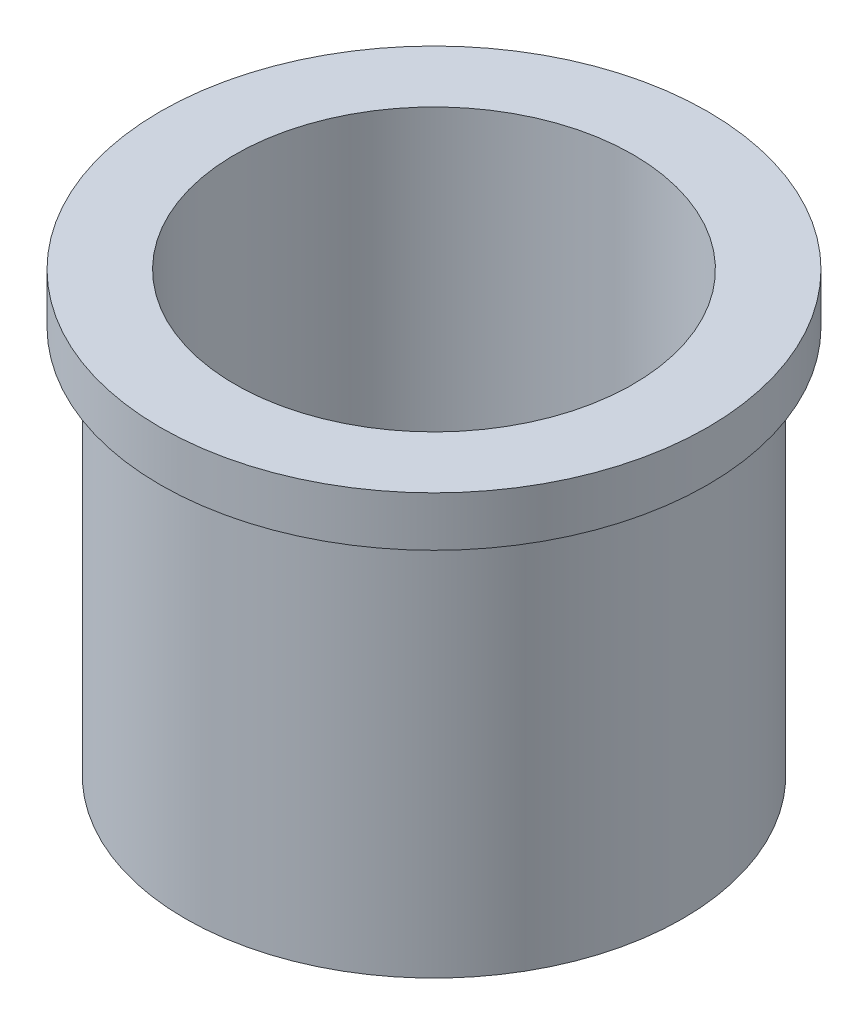
SolidWorks part; units mm, degrees
ref_plane "Front Plane" through (0, 0, 0) normal (0, 0, 1) x (1, 0, 0)
ref_plane "Top Plane" through (0, 0, 0) normal (0, 1, 0) x (1, 0, 0)
ref_plane "Right Plane" through (0, 0, 0) normal (1, 0, 0) x (0, 0, -1)
sketch "Sketch1" plane through (0, 0, 0) normal (0, 1, 0) x (1, 0, 0)
  circle A0 centre (0, 0) radius 12.7
  dimension "D2" = 25.4
extrude "Boss-Extrude1" add sketch "Sketch1" along normal blind 19.812
sketch "Sketch2" plane through (0, 19.812, 0) normal (0, 1, 0) x (1, 0, 0)
  circle A0 centre (0, 0) radius 13.97
  dimension "D1" = 27.94
extrude "Boss-Extrude2" add sketch "Sketch2" along normal blind 2.54
sketch "Sketch3" plane through (0, 0, 0) normal (0, -1, 0) x (1, 0, 0)
  circle A0 centre (0, 0) radius 10.16
  dimension "D1" = 20.32
extrude "Cut-Extrude1" cut sketch "Sketch3" against normal through all
